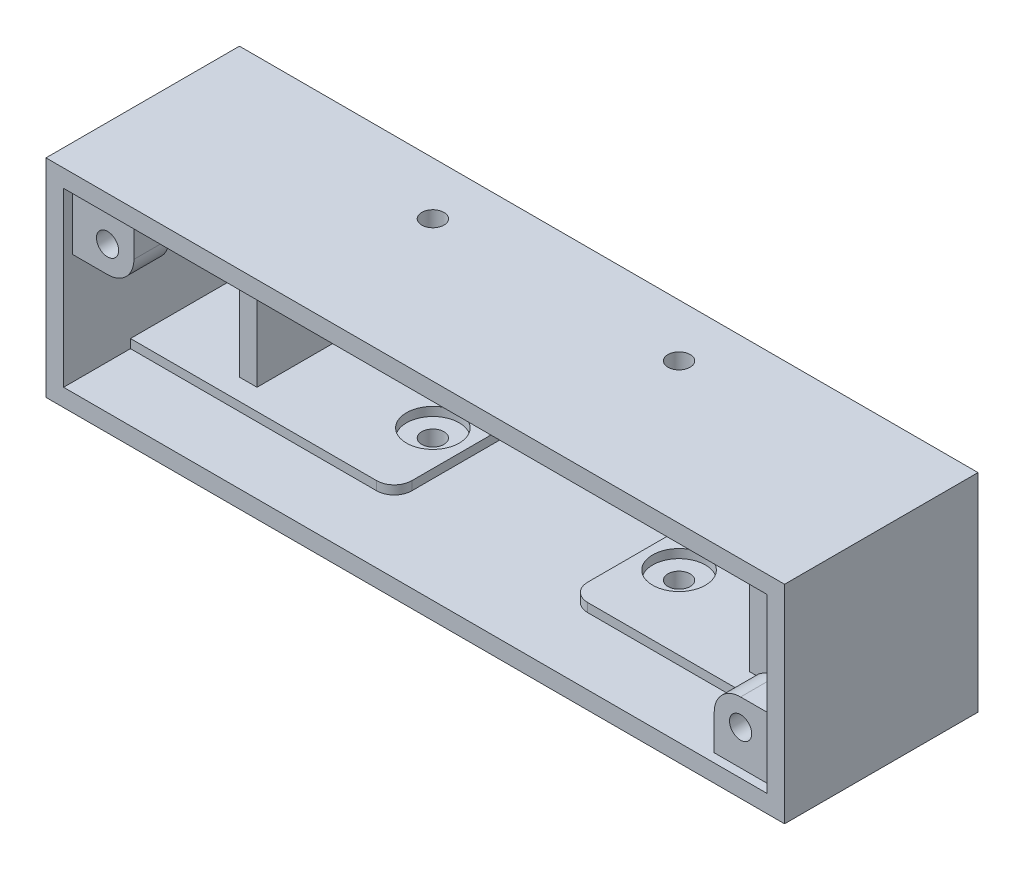
SolidWorks part; units mm, degrees
ref_plane "Front Plane" through (0, 0, 0) normal (0, 0, 1) x (1, 0, 0)
ref_plane "Top Plane" through (0, 0, 0) normal (0, 1, 0) x (1, 0, 0)
ref_plane "Right Plane" through (0, 0, 0) normal (1, 0, 0) x (0, 0, -1)
sketch "Sketch1" plane through (0, 0, 0) normal (0, 0, 1) x (1, 0, 0)
  line L1 (63.5, -15.5575) -> (-63.5, -15.5575)
  line L2 (63.5, -15.5575) -> (63.5, 15.5575)
  line L3 (63.5, 15.5575) -> (-63.5, 15.5575)
  line L4 (-63.5, -15.5575) -> (-63.5, 15.5575)
  line L5 (63.5, -15.5575) -> (-63.5, 15.5575) construction
  line L6 (63.5, 15.5575) -> (-63.5, -15.5575) construction
  point P0 (0, 0)
  dimension "D1" = 127
  dimension "D2" = 31.115
extrude "Boss-Extrude1" add sketch "Sketch1" along normal blind 3.175
sketch "Sketch2" plane through (0, 0, 3.175) normal (0, 0, 1) x (1, 0, 0)
  line L0 (-10, 0) -> (32, 0) construction
  line L1 (-10, 10.5) -> (32, 10.5)
  line L2 (-10, 10.5) -> (-10, -10.5)
  line L3 (-10, -10.5) -> (32, -10.5)
  line L4 (32, 10.5) -> (32, -10.5)
  line L6 (-13.2, 5) -> (35.2, 5) construction
  line L7 (-13.2, 5) -> (-13.2, -5) construction
  line L8 (-13.2, -5) -> (35.2, -5) construction
  line L9 (35.2, 5) -> (35.2, -5) construction
  circle A4 centre (-13.2, 5) radius 2
  circle A5 centre (-13.2, -5) radius 2
  circle A6 centre (35.2, 5) radius 2
  circle A7 centre (35.2, -5) radius 2
  point P11 (-13.2, 0)
  point P12 (11, 5)
  point P13 (11, 0)
  dimension "D6" = 4
  dimension "D1" = 42
  dimension "D2" = 21
  dimension "D3" = 10
  dimension "D4" = 10
  dimension "D5" = 48.4
extrude "Cut-Extrude1" cut sketch "Sketch2" against normal up to next
sketch "Sketch3" plane through (0, 0, 3.175) normal (0, 0, 1) x (1, 0, 0)
  line L1 (63.5, 15.5575) -> (-63.5, 15.5575)
  line L2 (63.5, 15.5575) -> (63.5, -15.5575)
  line L3 (63.5, -15.5575) -> (-63.5, -15.5575)
  line L4 (-63.5, 15.5575) -> (-63.5, -15.5575)
extrude "Extrude-Thin1" add sketch "Sketch3" along normal blind 31.75 and the other way up to surface (3.175 mm away) thin
sketch "Sketch4" plane through (0, 0, 3.175) normal (0, 0, 1) x (1, 0, 0)
  line L0 (63.5, -15.5575) -> (63.5, 15.5575) construction
  line L1 (-63.5, -15.5575) -> (-15.875, -15.5575)
  line L2 (-63.5, -15.5575) -> (-63.5, -13.97)
  line L3 (-63.5, -13.97) -> (-15.875, -13.97)
  line L4 (63.5, -15.5575) -> (63.5, -13.97)
  line L5 (63.5, -15.5575) -> (63.5, 15.5575) construction
  line L6 (-63.5, 15.5575) -> (-15.875, 15.5575)
  line L7 (-63.5, 15.5575) -> (-63.5, 13.97)
  line L8 (-63.5, 13.97) -> (-15.875, 13.97)
  line L9 (63.5, 15.5575) -> (63.5, 13.97)
  line L10 (-15.875, -13.97) -> (-15.875, -15.5575)
  line L12 (-15.875, 15.5575) -> (-15.875, 13.97)
  line L14 (15.875, 15.5575) -> (15.875, 13.97)
  line L15 (15.875, 13.97) -> (63.5, 13.97)
  line L16 (15.875, 15.5575) -> (63.5, 15.5575)
  line L17 (15.875, -13.97) -> (15.875, -15.5575)
  line L18 (15.875, -13.97) -> (63.5, -13.97)
  line L19 (15.875, -15.5575) -> (63.5, -15.5575)
  dimension "D1" = 1.5875
  dimension "D2" = 31.75
extrude "Boss-Extrude2" add sketch "Sketch4" along normal blind 19.675
sketch "Sketch6" plane through (0, 0, 3.175) normal (0, 0, 1) x (1, 0, 0)
  line L0 (-57.15, 9.2075) -> (57.15, -9.2075) construction
  line L6 (-66.675, 18.7325) -> (-66.675, -18.7325) construction
  line L8 (66.675, 18.7325) -> (-66.675, 18.7325) construction
  circle A1 centre (-57.15, 9.2075) radius 4.7625
  circle A2 centre (57.15, -9.2075) radius 4.7625
  point P3 (0, 0)
  dimension "D2" = 9.525
  dimension "D3" = 9.525
  dimension "D1" = 9.525
extrude "Cut-Extrude2" cut sketch "Sketch6" against normal up to next
sketch "Sketch7" plane through (0, 0, 34.925) normal (0, 0, 1) x (1, 0, 0)
  line L0 (-63.5, 15.5575) -> (-63.5, 4.445)
  line L1 (-63.5, 15.5575) -> (-63.5, -15.5575) construction
  line L2 (-63.5, 4.445) -> (-57.15, 4.445)
  line L3 (-52.3875, 9.2075) -> (-52.3875, 15.5575)
  line L4 (-15.875, 15.5575) -> (-63.5, 15.5575) construction
  line L5 (-52.3875, 15.5575) -> (-63.5, 15.5575)
  line L6 (63.5, -15.5575) -> (52.3875, -15.5575)
  line L7 (-63.5, -15.5575) -> (63.5, -15.5575) construction
  line L8 (52.3875, -15.5575) -> (52.3875, -9.2075)
  line L9 (57.15, -4.445) -> (63.5, -4.445)
  line L10 (63.5, -13.97) -> (63.5, 13.97) construction
  line L11 (63.5, -4.445) -> (63.5, -15.5575)
  arc A0 (-57.15, 4.445) -> (-52.3875, 9.2075) centre (-57.15, 9.2075) ccw
  arc A3 (52.3875, -9.2075) -> (57.15, -4.445) centre (57.15, -9.2075) cw
  circle A5 centre (-57.15, 9.2075) radius 4.7625 construction
  circle A6 centre (57.15, -9.2075) radius 4.7625 construction
  dimension "D1" = 4.7625
extrude "Boss-Extrude4" add sketch "Sketch7" against normal blind 6.35 from offset 1.5875 offset against normal yes
sketch "Sketch8" plane through (0, 0, 34.925) normal (0, 0, 1) x (1, 0, 0)
  circle A0 centre (-57.15, 9.2075) radius 2
  circle A1 centre (57.15, -9.2075) radius 2
  dimension "D1" = 4
extrude "Cut-Extrude3" cut sketch "Sketch8" against normal up to next
sketch "Sketch9" plane through (0, 0, 0) normal (0, 1, 0) x (1, 0, 0)
  line L0 (-22.225, -9.525) -> (22.225, -9.525) construction
  line L1 (-66.675, 0) -> (66.675, 0) construction
  circle A0 centre (22.225, -9.525) radius 2
  circle A1 centre (-22.225, -9.525) radius 2
  point P2 (0, -9.525)
  dimension "D3" = 4
  dimension "D1" = 9.525
  dimension "D2" = 44.45
extrude "Cut-Extrude4" cut sketch "Sketch9" against normal through all both and the other way through all
sketch "Sketch5" plane through (0, 0, 3.175) normal (0, 0, 1) x (1, 0, 0)
  line L0 (-63.5, 13.97) -> (-57.15, 13.97) construction
  line L1 (44.45, 13.97) -> (47.625, 13.97)
  line L2 (44.45, 13.97) -> (44.45, -13.97)
  line L3 (44.45, -13.97) -> (47.625, -13.97)
  line L4 (47.625, 13.97) -> (47.625, -13.97)
  line L5 (-15.875, -13.97) -> (-63.5, -13.97) construction
  line L6 (-63.5, 13.97) -> (-15.875, 13.97) construction
  line L7 (-47.625, 13.97) -> (-44.45, 13.97)
  line L8 (-47.625, 13.97) -> (-47.625, -13.97)
  line L9 (-47.625, -13.97) -> (-44.45, -13.97)
  line L10 (-44.45, 13.97) -> (-44.45, -13.97)
  line L11 (-44.45, 0) -> (44.45, 0) construction
  point P16 (0, 0)
  dimension "D1" = 3.175
  dimension "D2" = 44.45
extrude "Boss-Extrude3" add sketch "Sketch5" along normal blind 15.875
fillet "Fillet1" radius 3.175 4 edges at (-15.875, 14.7637, 22.85) (15.875, 14.7637, 22.85) (15.875, -14.7638, 22.85) (-15.875, -14.7638, 22.85)
sketch "Sketch10" plane through (0, 0, 0) normal (0, 1, 0) x (1, 0, 0)
  circle A0 centre (-22.225, -9.525) radius 4.7625
  circle A1 centre (22.225, -9.525) radius 4.7625
  dimension "D1" = 9.525
extrude "Cut-Extrude5" cut sketch "Sketch10" against normal up to surface and the other way up to surface up to face at (16.5554, -15.5575, 23.4939) other way up to face at (-16.5554, 15.5575, 23.4939)
